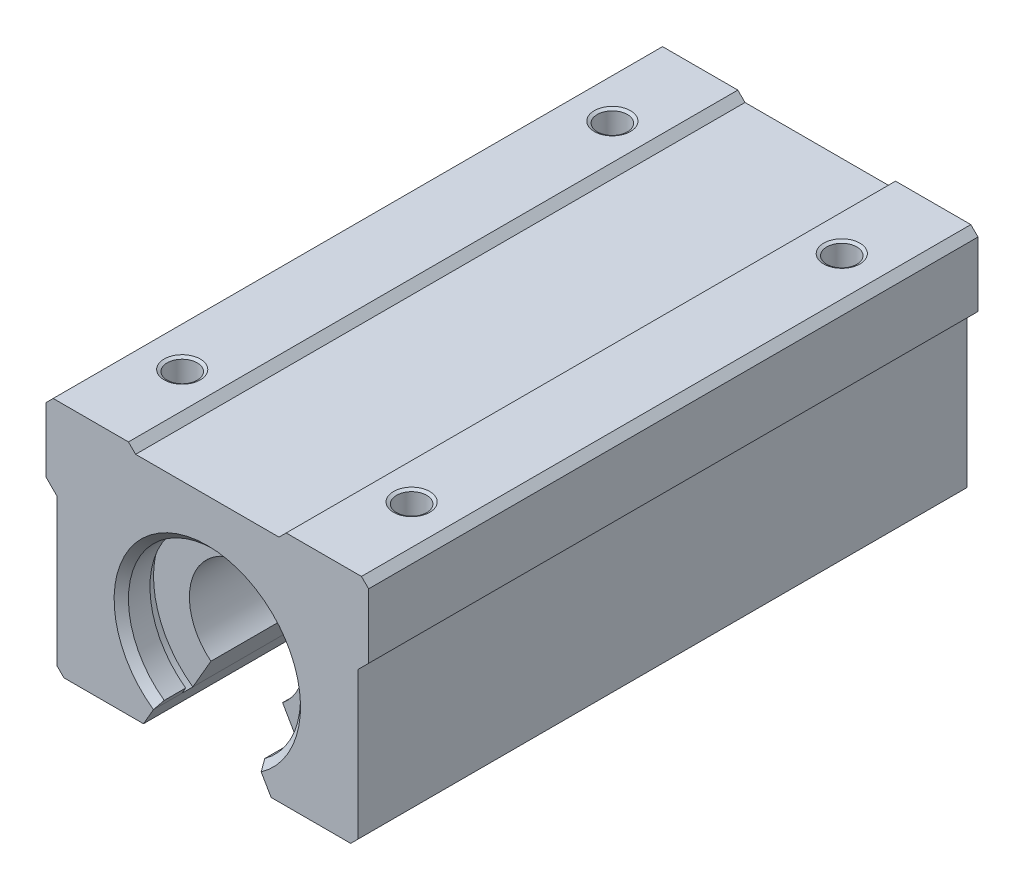
SolidWorks part; units mm, degrees
ref_plane "Front Plane" through (0, 0, 0) normal (0, 0, 1) x (1, 0, 0)
ref_plane "Top Plane" through (0, 0, 0) normal (0, 1, 0) x (1, 0, 0)
ref_plane "Right Plane" through (0, 0, 0) normal (1, 0, 0) x (0, 0, -1)
sketch "Sketch1" plane through (0, 0, 0) normal (0, 0, 1) x (1, 0, 0)
  line L0 (0, 0) -> (-148.4889, 0) construction
  line L1 (0, 0) -> (174.9125, 0) construction
  line L2 (0, 0) -> (0, 19) construction
  line L3 (0, 0) -> (0, -105.9815) construction
  line L4 (0, 0) -> (0, 1.733) construction
  line L5 (0, 0) -> (0, 20) construction
  line L6 (10, 19) -> (-10, 19)
  line L7 (0, 20) -> (-27.817, 20) construction
  line L8 (-10, 19) -> (-11, 20)
  line L9 (-11, 20) -> (-22.5, 20)
  line L10 (-22.5, 20) -> (-22.5, 10)
  line L11 (-22.5, 10) -> (-21, 10) construction
  line L12 (-21, 10) -> (-21, 2.1484) construction
  line L13 (-22.5, 10) -> (-21, 8.5)
  line L14 (-21, 8.5) -> (-21, -13)
  line L15 (-21, -13) -> (18.4801, -13) construction
  line L16 (-21, -13) -> (-8.9, -13)
  line L17 (-8.9, -13) -> (-5, -6.245)
  line L18 (8.9, -13) -> (5, -6.245)
  line L19 (21, -13) -> (8.9, -13)
  line L20 (21, 8.5) -> (21, -13)
  line L21 (22.5, 10) -> (21, 8.5)
  line L22 (22.5, 20) -> (22.5, 10)
  line L23 (11, 20) -> (22.5, 20)
  line L24 (10, 19) -> (11, 20)
  arc A0 (5, -6.245) -> (-5, -6.245) centre (0, 0) ccw
  dimension "D1" = 1
  dimension "D2" = 16
  dimension "D3" = 1.5
  dimension "D4" = 1.5
  dimension "D5" = 33
  dimension "D6" = 10
  dimension "D7" = 22.5
  dimension "D8" = 1
  dimension "D9" = 10
  dimension "D10" = 20
  dimension "D11" = 12.1
  dimension "D12" = 60
extrude "Boss-Extrude1" add sketch "Sketch1" along normal blind 85
chamfer "Chamfer2" distance 1 angle 45 1 edges at (-22.5, 20, 42.5)
chamfer "Chamfer3" distance 1 angle 45 3 edges at (22.5, 20, 42.5) (21, -13, 42.5) (-21, -13, 42.5)
sketch "Sketch4" plane through (0, 20, 0) normal (0, 1, 0) x (1, 0, 0)
  line L0 (-21.5, -42.5) -> (30.5184, -42.5) construction
  line L1 (0, 0) -> (-16, 0) construction
  line L2 (-11, 0) -> (-21.5, 0) construction
  line L3 (-16, 0) -> (-16, -29.5588) construction
  line L4 (-21.5, 0) -> (-21.5, -85) construction
  line L5 (0, 0) -> (0, -85) construction
  line L6 (10, -85) -> (-10, -85) construction
  line L7 (-21.5, -42.5) -> (-21.5, -12.5) construction
  line L8 (-21.5, -12.5) -> (-16, -12.5) construction
  line L9 (-11, -85) -> (-21.5, -85) construction
  point P10 (16, -12.5)
  point P16 (16, -72.5)
  point P17 (-16, -72.5)
  dimension "D1" = 30
  dimension "D2" = 16
hole_wizard "M5 Tapped Hole1" positions "3DSketch1" profile "Sketch5" tap size "M5" standard "GB"
sketch3d "3DSketch1"
  point P0 (-16, 20, 12.5)
  point P3 (16, 20, 12.5)
  point P6 (-16, 20, 72.5)
  point P9 (16, 20, 72.5)
sketch "Sketch5" plane through (-16, 20, 12.5) normal (1, 0, 0) x (0, 0, 1)
  line L0 (0, 0) -> (0, 13.2618)
  line L1 (0, 13.2618) -> (2.1, 12)
  line L2 (2.1, 12) -> (2.1, 0.2454)
  line L3 (2.1, 0.2454) -> (2.525, 0)
  line L5 (2.525, 0) -> (0, 0)
  line L6 (-2.1, 0.2454) -> (-2.525, 0) construction
  line L10 (0, 13.2618) -> (-2.1, 12) construction
  line L11 (0, -6.35) -> (0, 107.95) construction
  dimension "Tap Drill Dia." = 4.2
  dimension "Tap Drill Depth" = 12
  dimension "Near C'Sink Dia." = 5.05
  dimension "Near C'Sink Angle" = 120
  dimension "Drill Angle" = 118
cosmetic thread "Hole Thread1" parameters "D1"=9, "D2"=5
cosmetic thread "Hole Thread2" parameters "D1"=9, "D2"=5
cosmetic thread "Hole Thread3" parameters "D1"=9, "D2"=5
cosmetic thread "Hole Thread4" parameters "D1"=9, "D2"=5
sketch "Sketch6" plane through (0, 0, 85) normal (0, 0, 1) x (1, 0, 0)
  circle A0 centre (0, 0) radius 12
  arc A1 (5, -6.245) -> (-5, -6.245) centre (0, 0) ccw construction
  dimension "D1" = 4
extrude "Cut-Extrude1" cut sketch "Sketch6" against normal blind 4
sketch "Sketch7" plane through (0, 0, 0) normal (0, 0, -1) x (-1, 0, 0)
  circle A0 centre (0, 0) radius 12
  arc A1 (5, -6.245) -> (-5, -6.245) centre (0, 0) ccw construction
  dimension "D1" = 4
extrude "Cut-Extrude2" cut sketch "Sketch7" against normal blind 4
chamfer "Chamfer5" distance 1 angle 45 2 edges at (0, 12, 0) (0, 12, 85)
ref_plane "Plane3" through (0, 0, 81) normal (0, 0, 1) x (1, 0, 0)
sketch "Sketch12" plane through (0, 0, 81) normal (0, 0, 1) x (1, 0, 0)
  circle A0 centre (0, 0) radius 13
  dimension "D1" = 26
extrude "Cut-Extrude7" cut sketch "Sketch12" against normal blind 1.5
ref_plane "Plane4" through (0, 0, 4) normal (0, 0, -1) x (-1, 0, 0)
sketch "Sketch13" plane through (0, 0, 4) normal (0, 0, -1) x (-1, 0, 0)
  circle A0 centre (0, 0) radius 13
  dimension "D1" = 26
extrude "Cut-Extrude8" cut sketch "Sketch13" against normal blind 1.5
sketch "Sketch14" plane through (0, 0, 85) normal (0, 0, 1) x (1, 0, 0)
  line L0 (7.5177, -10.6058) -> (21, -10.6058)
  line L1 (21, -12) -> (21, 8.5) construction
  line L2 (7.5177, -10.6058) -> (-7.5177, -10.6058)
  line L3 (-7.5177, -10.6058) -> (-21, -10.6058)
  line L4 (-21, 8.5) -> (-21, -12) construction
split line "Split Line2"
